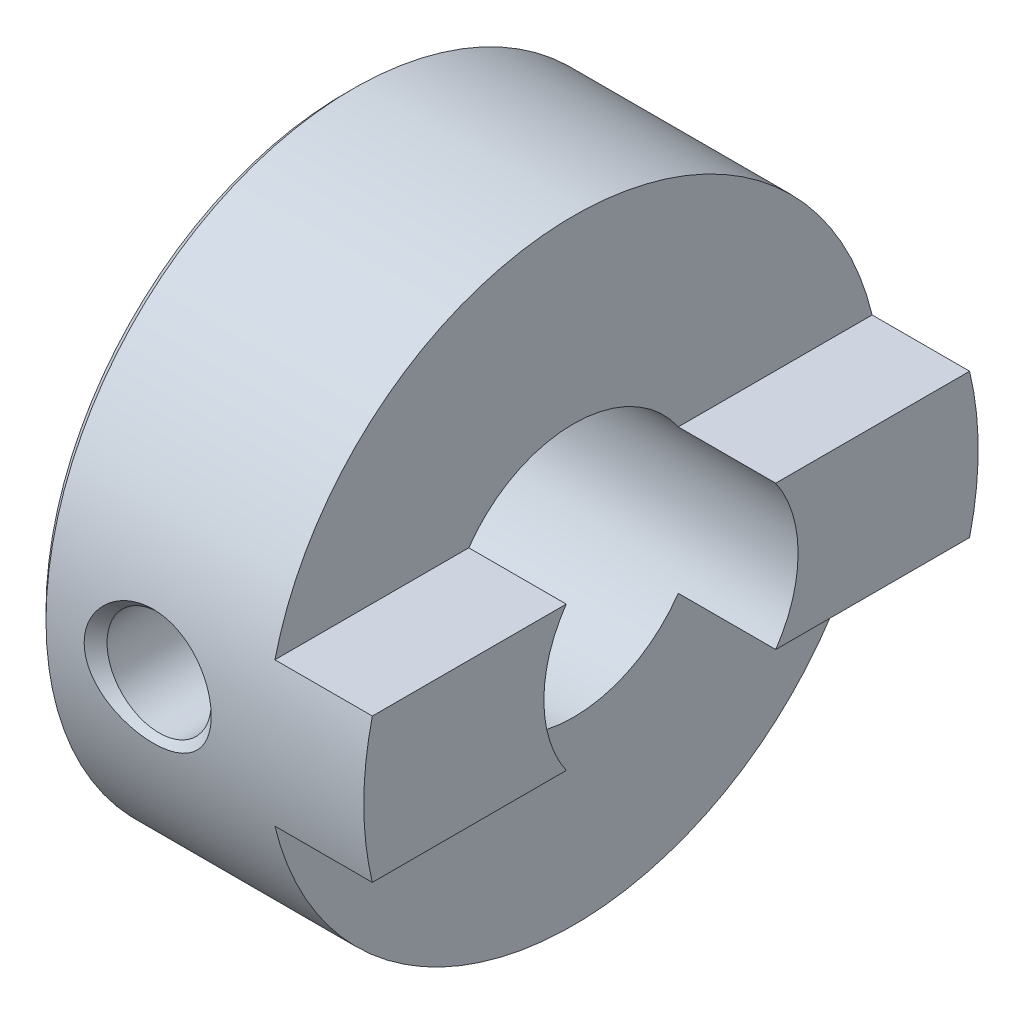
SolidWorks part; units mm, degrees
ref_plane "Front Plane" through (0, 0, 0) normal (0, 0, 1) x (1, 0, 0)
ref_plane "Top Plane" through (0, 0, 0) normal (0, 1, 0) x (1, 0, 0)
ref_plane "Right Plane" through (0, 0, 0) normal (1, 0, 0) x (0, 0, -1)
ref_plane "Plane1" through (0, 0, 0) normal (0, 0, 1) x (1, 0, 0)
sketch "Sketch1" plane through (0, 0, 0) normal (0, 0, 1) x (1, 0, 0)
  line L0 (0, 7.05) -> (0, 3)
  line L1 (0, 3) -> (7.7, 3)
  line L2 (7.7, 3) -> (7.7, 7.25)
  line L3 (7.7, 7.25) -> (0.2, 7.25)
  line L4 (0.2, 7.25) -> (0, 7.05)
  line L5 (7.7, 0) -> (0, 0) construction
revolve "Revolve1" add sketch "Sketch1" angle 360 about L5
ref_plane "Plane2" through (7.7, 0, 0) normal (1, 0, 0) x (0, 0, -1)
sketch "Sketch2" plane through (7.7, 0, 0) normal (1, 0, 0) x (0, 0, -1)
  line L0 (-8.25, 7.75) -> (-8.25, -7.75)
  line L1 (-8.25, -7.75) -> (8.25, -7.75)
  line L2 (8.25, -7.75) -> (8.25, 7.75)
  line L3 (8.25, 7.75) -> (-8.25, 7.75)
  line L4 (-7.25, 1.7) -> (-7.25, -1.7)
  line L5 (-7.25, -1.7) -> (7.25, -1.7)
  line L6 (7.25, -1.7) -> (7.25, 1.7)
  line L7 (7.25, 1.7) -> (-7.25, 1.7)
extrude "Cut-Extrude1" cut sketch "Sketch2" against normal blind 2.3
ref_plane "Plane3" through (2.6, 0, 0) normal (1, 0, 0) x (0, 0, -1)
sketch "Sketch3" plane through (2.6, 0, 0) normal (1, 0, 0) x (0, 0, -1)
  line L0 (-7.25, 0) -> (-7.25, 1.5)
  line L1 (-7.25, 1.5) -> (-6.9795, 1.2295)
  line L2 (-6.9795, 1.2295) -> (0, 1.2295)
  line L3 (0, 1.2295) -> (0, 0)
  line L4 (0, 0) -> (-7.25, 0)
  line L5 (0, 0) -> (-7.25, 0) construction
revolve "Cut-Revolve1" cut sketch "Sketch3" angle 360 about L5
ref_plane "Plane4" through (2.6, 0, 0) normal (1, 0, 0) x (0, 0, -1)
sketch "Sketch4" plane through (2.6, 0, 0) normal (1, 0, 0) x (0, 0, -1)
  line L0 (0, -7.25) -> (-1.5, -7.25)
  line L1 (-1.5, -7.25) -> (-1.2295, -6.9795)
  line L2 (-1.2295, -6.9795) -> (-1.2295, 0)
  line L3 (-1.2295, 0) -> (0, 0)
  line L4 (0, 0) -> (0, -7.25)
  line L5 (0, 0) -> (0, -7.25) construction
revolve "Cut-Revolve2" cut sketch "Sketch4" angle 360 about L5
